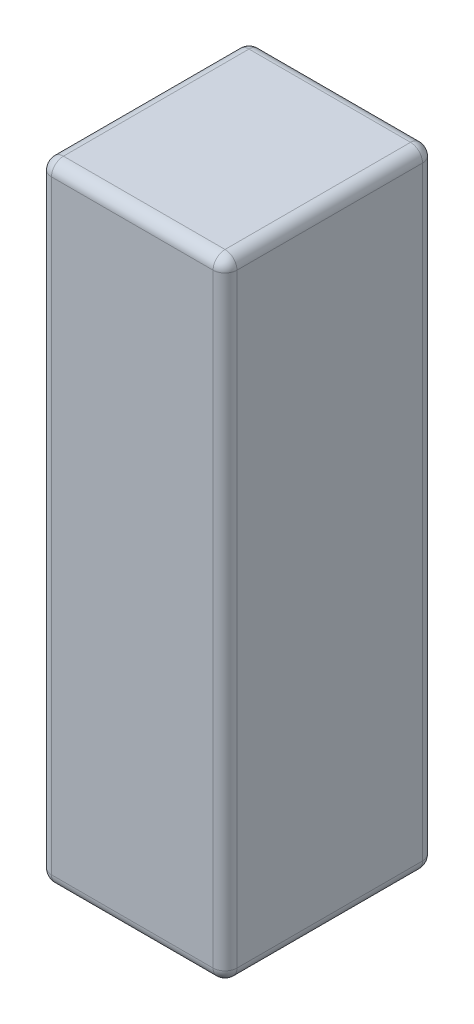
SolidWorks part; units mm, degrees
ref_plane "Front Plane" through (0, 0, 0) normal (0, 0, 1) x (1, 0, 0)
ref_plane "Top Plane" through (0, 0, 0) normal (0, 1, 0) x (1, 0, 0)
ref_plane "Right Plane" through (0, 0, 0) normal (1, 0, 0) x (0, 0, -1)
sketch "Sketch1" plane through (0, 0, 0) normal (0, 1, 0) x (1, 0, 0)
  line L1 (0, 0) -> (31, 0)
  line L2 (0, 0) -> (0, 35)
  line L3 (0, 35) -> (31, 35)
  line L4 (31, 0) -> (31, 35)
  dimension "D1" = 31
  dimension "D2" = 35
extrude "Boss-Extrude1" add sketch "Sketch1" along normal blind 105
fillet "Fillet1" radius 2 12 edges at (15.5, 0, 0) (31, 0, -17.5) (15.5, 0, -35) (0, 0, -17.5) (15.5, 105, -35) (31, 105, -17.5) (15.5, 105, 0) (0, 105, -17.5) (31, 52.5, -35) (0, 52.5, -35) (0, 52.5, 0) (31, 52.5, 0)
